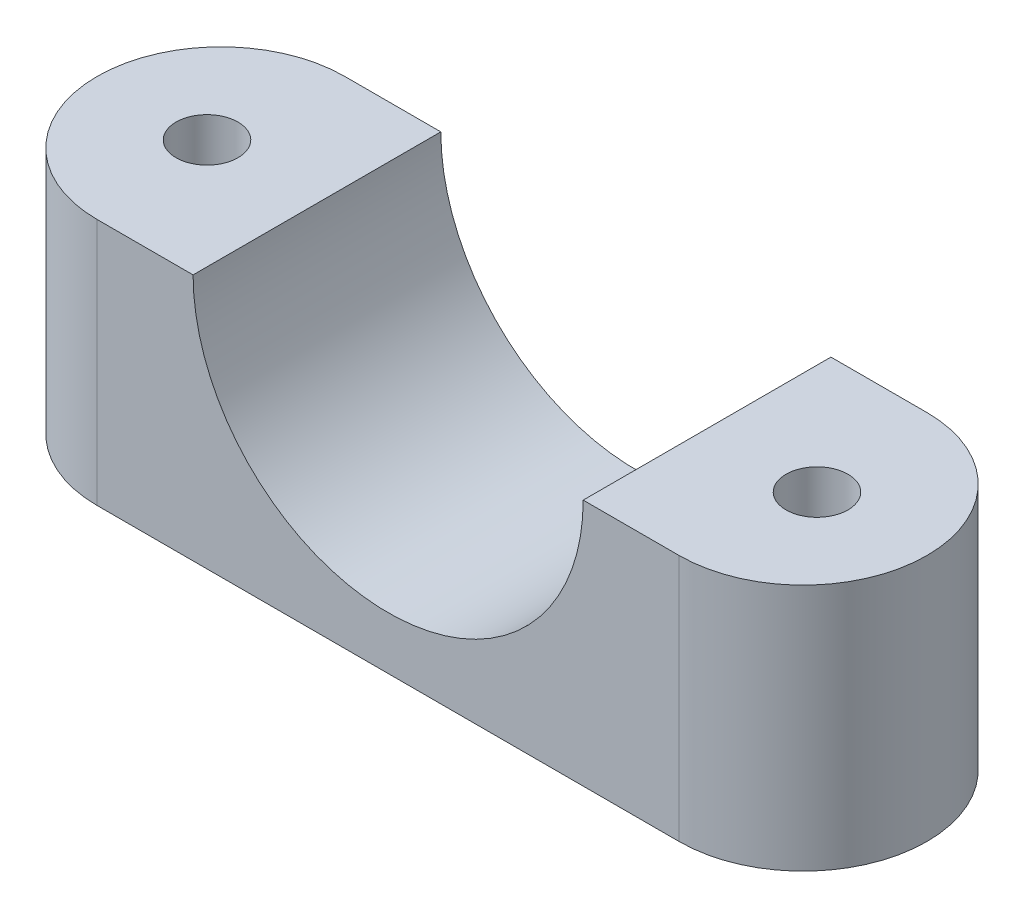
SolidWorks part; units mm, degrees
material "6061 Alloy"
ref_plane "Front Plane" through (0, 0, 0) normal (0, 0, 1) x (1, 0, 0)
ref_plane "Top Plane" through (0, 0, 0) normal (0, 1, 0) x (1, 0, 0)
ref_plane "Right Plane" through (0, 0, 0) normal (1, 0, 0) x (0, 0, -1)
sketch "Sketch1" plane through (0, 0, 0) normal (0, 0, 1) x (1, 0, 0)
  line L0 (-45.5169, 0) -> (71.0826, 0) construction
  line L1 (0, -30.4417) -> (0, 38.0802) construction
  line L2 (-20, 0) -> (-42.545, 0)
  line L3 (-42.545, 0) -> (-42.545, -25.4)
  line L4 (-42.545, -25.4) -> (42.545, -25.4)
  line L5 (42.545, 0) -> (42.545, -25.4)
  line L6 (20, 0) -> (42.545, 0)
  arc A0 (-20, 0) -> (20, 0) centre (0, 0) ccw
  point P12 (0, -25.4)
  dimension "D1" = 40
  dimension "D2" = 25.4
  dimension "D3" = 42.545
extrude "Boss-Extrude1" add sketch "Sketch1" along normal mid plane 25.4
sketch "Sketch2" plane through (0, 0, 0) normal (0, 1, 0) x (1, 0, 0)
  line L0 (-42.545, 12.7) -> (-20, -12.7) construction
  circle A0 centre (-31.2725, 0) radius 3.175
  dimension "D1" = 6.35
extrude "Cut-Extrude1" cut sketch "Sketch2" against normal through all
mirror "Mirror1" about plane through (0, 0, 0) normal (1, 0, 0) of "Cut-Extrude1"
sketch "Sketch3" plane through (0, -25.4, 0) normal (0, -1, 0) x (1, 0, 0)
  line L0 (-42.545, 12.7) -> (-42.545, -12.7) construction
  line L1 (-29.845, -12.7) -> (-29.845, 12.7) construction
  line L2 (-42.545, 12.7) -> (42.545, 12.7) construction
  line L3 (-42.545, -12.7) -> (42.545, -12.7) construction
  line L4 (0, -14.5802) -> (0, 16.4976) construction
  line L5 (-29.845, 12.7) -> (29.845, 12.7)
  line L6 (29.845, -12.7) -> (-29.845, -12.7)
  arc A0 (-29.845, 12.7) -> (-29.845, -12.7) centre (-29.845, 0) ccw
  arc A1 (29.845, 12.7) -> (29.845, -12.7) centre (29.845, 0) cw
extrude "Cut-Extrude4" cut sketch "Sketch3" against normal blind 25.4 flip side to cut
